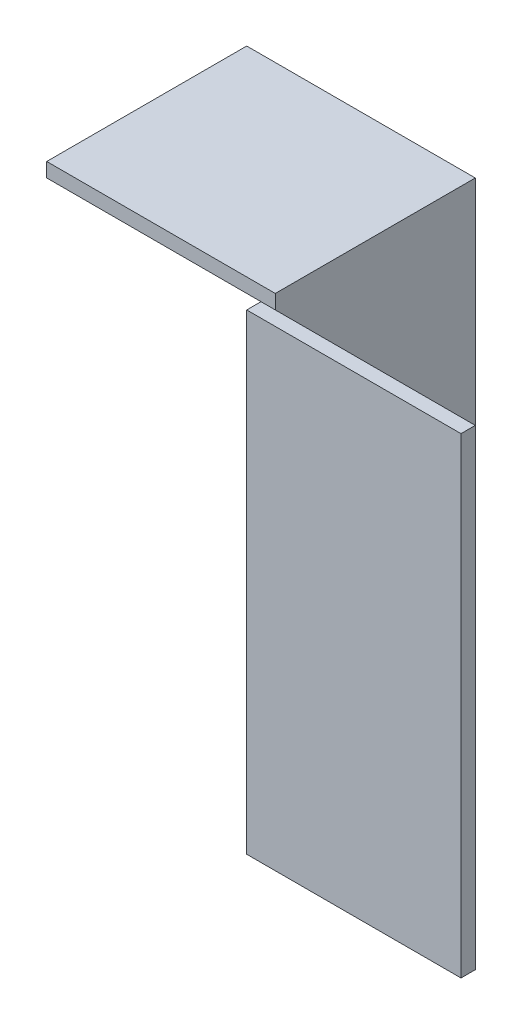
SolidWorks part; units mm, degrees
material "1060 Сплав"
ref_plane "Спереди" through (0, 0, 0) normal (0, 0, 1) x (1, 0, 0)
ref_plane "Сверху" through (0, 0, 0) normal (0, 1, 0) x (1, 0, 0)
ref_plane "Справа" through (0, 0, 0) normal (1, 0, 0) x (0, 0, -1)
sketch "Эскиз1" plane through (0, 0, 0) normal (0, 1, 0) x (1, 0, 0)
  line L0 (0, 0) -> (0, 15)
  line L1 (0, 15) -> (1, 15)
  line L2 (1, 15) -> (1, 1)
  line L3 (1, 1) -> (15, 1)
  line L4 (15, 1) -> (15, 0)
  line L5 (15, 0) -> (0, 0)
  dimension "D1" = 1
  dimension "D2" = 15
extrude "Бобышка-Вытянуть1" add sketch "Эскиз1" along normal blind 53
sketch "Эскиз5" plane through (0, 53, 0) normal (0, 1, 0) x (1, 0, 0)
  line L6 (0, 0) -> (15, 0)
  line L7 (15, 0) -> (15, 1)
  line L8 (15, 1) -> (1, 1)
  line L9 (1, 1) -> (1, 15)
  line L10 (1, 15) -> (0, 15)
  line L11 (0, 15) -> (0, 0)
  line L12 (0, 0) -> (15, 0)
  line L13 (15, 0) -> (15, 1)
  line L14 (15, 1) -> (1, 1)
  line L15 (1, 1) -> (1, 15)
  line L16 (1, 15) -> (0, 15)
  line L17 (0, 15) -> (0, 0)
  dimension "D1" = 0
extrude "Вырез-Вытянуть2" cut sketch "Эскиз5" against normal blind 20
sketch "Эскиз6" plane through (1, 0, 0) normal (1, 0, 0) x (0, 0, -1)
  line L0 (15, 33) -> (1, 33)
  line L1 (15, 33) -> (15, 34)
  line L2 (1, 33) -> (1, 34)
  line L3 (15, 34) -> (1, 34)
  dimension "D1" = 1
extrude "Бобышка-Вытянуть2" add sketch "Эскиз6" against normal blind 16
